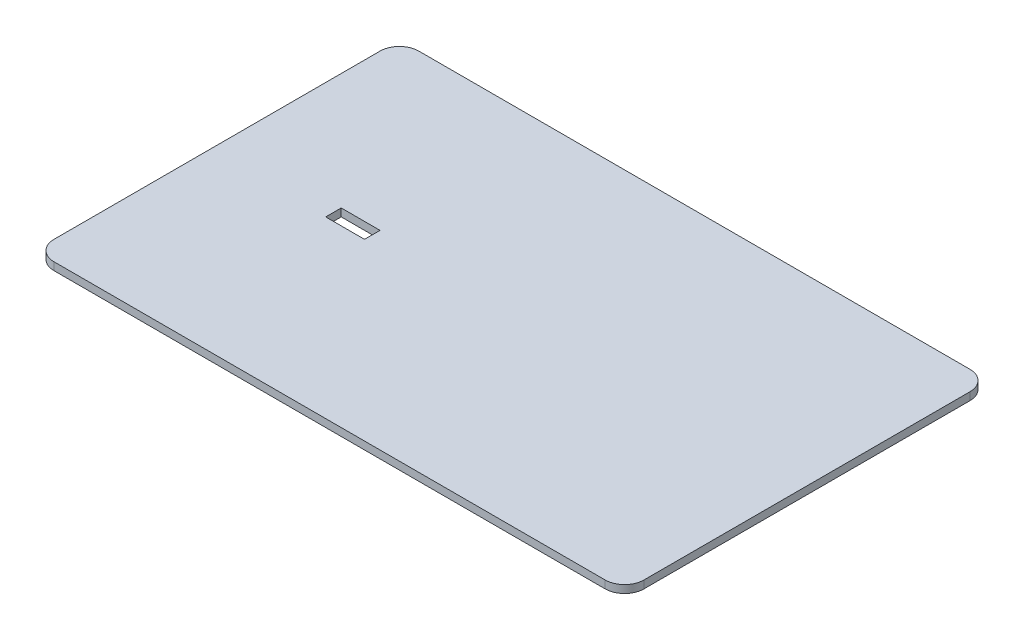
SolidWorks part; units mm, degrees
ref_plane "Front Plane" through (0, 0, 0) normal (0, 0, 1) x (1, 0, 0)
ref_plane "Top Plane" through (0, 0, 0) normal (0, 1, 0) x (1, 0, 0)
ref_plane "Right Plane" through (0, 0, 0) normal (1, 0, 0) x (0, 0, -1)
sketch "Sketch1" plane through (0, 0, 0) normal (0, 1, 0) x (1, 0, 0)
  line L1 (-38, 23.5) -> (38, 23.5)
  line L2 (-38, 23.5) -> (-38, -23.5)
  line L3 (-38, -23.5) -> (38, -23.5)
  line L4 (38, 23.5) -> (38, -23.5)
  line L5 (-38, 23.5) -> (38, -23.5) construction
  line L6 (-38, -23.5) -> (38, 23.5) construction
  point P0 (0, 0)
  dimension "D1" = 76
  dimension "D2" = 47
extrude "Boss-Extrude1" add sketch "Sketch1" against normal blind 1
sketch "Sketch2" plane through (0, -1, 0) normal (0, -1, 0) x (1, 0, 0)
  line L0 (-30.5, 18) -> (30.5, 18)
  line L1 (-33, 20.5) -> (33, 20.5)
  line L2 (-33, 20.5) -> (-33, -20.5)
  line L3 (-33, -20.5) -> (33, -20.5)
  line L4 (33, 20.5) -> (33, -20.5)
  line L5 (-33, 20.5) -> (33, -20.5) construction
  line L6 (-33, -20.5) -> (33, 20.5) construction
  line L7 (30.5, 18) -> (30.5, -18)
  line L8 (-30.5, -18) -> (30.5, -18)
  line L9 (-30.5, 18) -> (-30.5, -18)
  point P0 (0, 0)
  dimension "D1" = 66
  dimension "D2" = 41
  dimension "D3" = 2.5
extrude "Boss-Extrude2" add sketch "Sketch2" along normal blind 2.5
fillet "Fillet1" radius 2.5 4 edges at (38, -0.5, -23.5) (-38, -0.5, -23.5) (38, -0.5, 23.5) (-38, -0.5, 23.5)
sketch "Sketch4" plane through (0, 0, 0) normal (0, 1, 0) x (1, 0, 0)
  line L1 (-23, 1) -> (-18, 1)
  line L2 (-23, 1) -> (-23, -1)
  line L3 (-23, -1) -> (-18, -1)
  line L4 (-18, 1) -> (-18, -1)
  line L5 (-23, 1) -> (-18, -1) construction
  line L6 (-23, -1) -> (-18, 1) construction
  line L7 (-38, 21) -> (-38, -21) construction
  point P0 (-20.5, 0)
  dimension "D1" = 5
  dimension "D2" = 2
  dimension "D3" = 17.5
extrude "Cut-Extrude1" cut sketch "Sketch4" against normal up to surface (1 mm away) up to face at (0, -1, 0)
